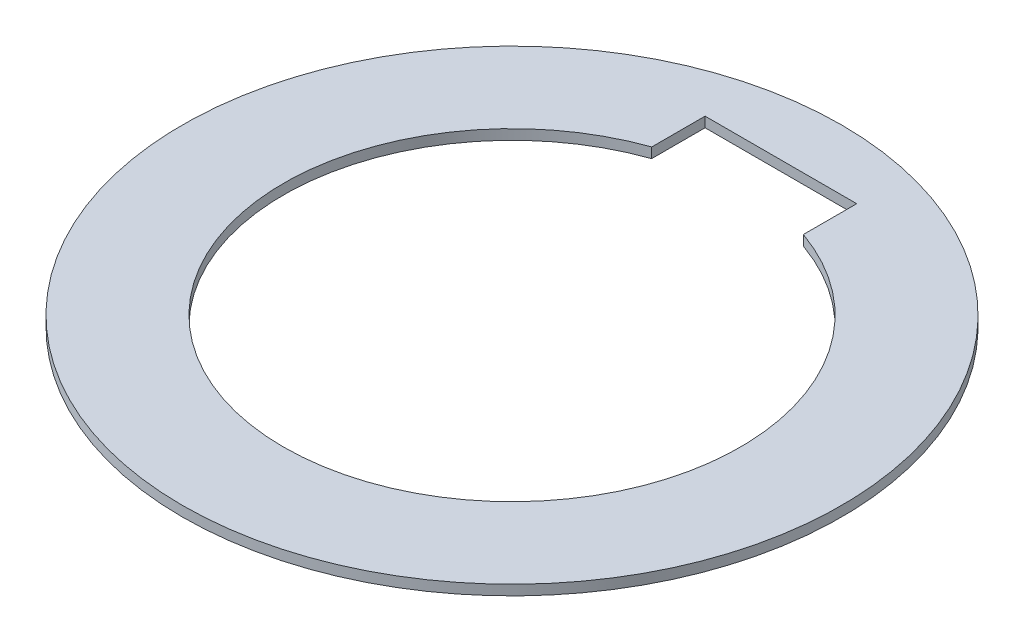
SolidWorks part; units mm, degrees
ref_plane "Alzado" through (0, 0, 0) normal (0, 0, 1) x (1, 0, 0)
ref_plane "Planta" through (0, 0, 0) normal (0, 1, 0) x (1, 0, 0)
ref_plane "Vista lateral" through (0, 0, 0) normal (1, 0, 0) x (0, 0, -1)
sketch "Sketch1" plane through (0, 0, 0) normal (0, 1, 0) x (1, 0, 0)
  line L0 (-7.5, 26.6) -> (-7.5, 21.3192)
  line L1 (7.5, 26.6) -> (7.5, 21.3192)
  line L2 (-7.5, 30.147) -> (-7.5, 24.7982) construction
  line L3 (7.5, 30.147) -> (7.5, 24.7982) construction
  line L4 (-7.5, 26.6) -> (7.5, 26.6)
  circle A0 centre (0, 0) radius 32.6
  arc A1 (-7.5, 21.3192) -> (7.5, 21.3192) centre (0, 0) ccw
  arc A2 (-7.5, 21.3192) -> (7.5, 21.3192) centre (0, 0) cw construction
  point P0 (0, 22.6)
  dimension "D1" = 45.2
  dimension "D2" = 10
  dimension "D4" = 4
  dimension "D3" = 15
extrude "Extrude1" add sketch "Sketch1" along normal blind 1
